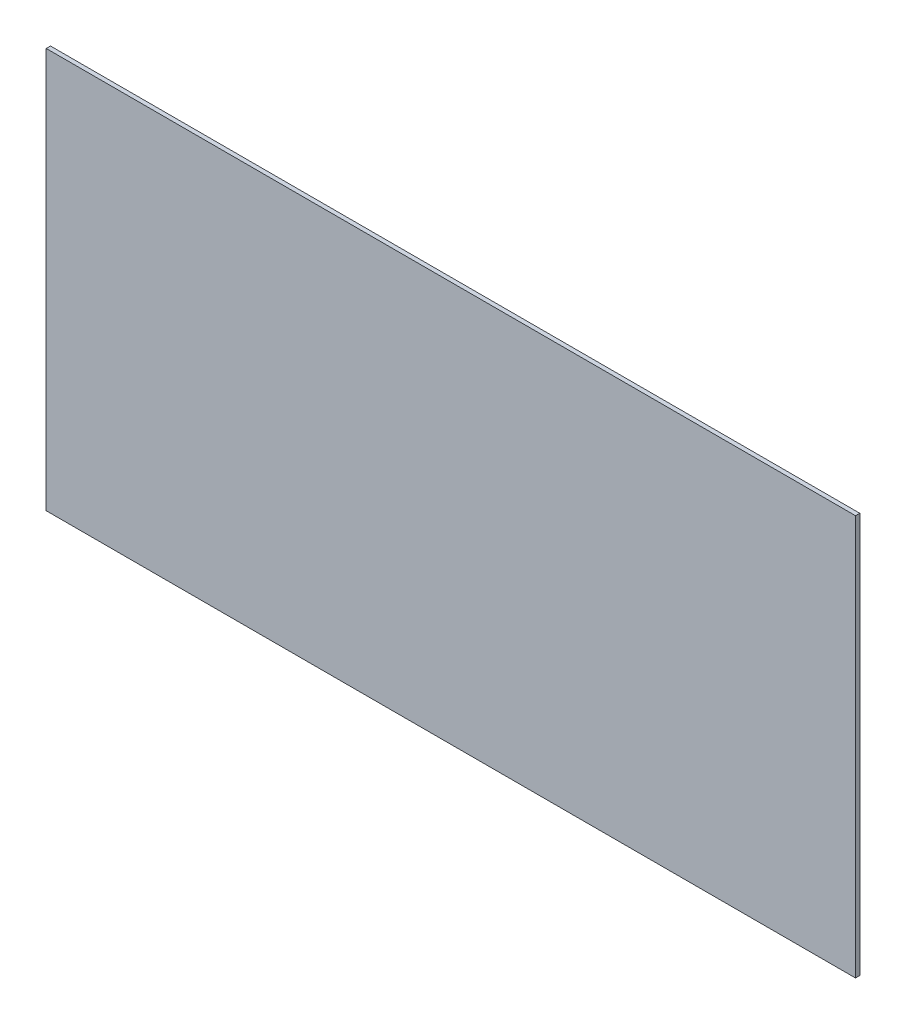
SolidWorks part; units mm, degrees
ref_plane "Front Plane" through (0, 0, 0) normal (0, 0, 1) x (1, 0, 0)
ref_plane "Top Plane" through (0, 0, 0) normal (0, 1, 0) x (1, 0, 0)
ref_plane "Right Plane" through (0, 0, 0) normal (1, 0, 0) x (0, 0, -1)
sketch "Sketch1" plane through (0, 0, 0) normal (0, 0, 1) x (1, 0, 0)
  line L1 (603.25, 298.45) -> (0, 298.45)
  line L2 (603.25, 298.45) -> (603.25, 0)
  line L3 (603.25, 0) -> (0, 0)
  line L4 (0, 298.45) -> (0, 0)
  dimension "D1" = 603.25
  dimension "D2" = 298.45
extrude "Boss-Extrude1" add sketch "Sketch1" along normal blind 3.175
